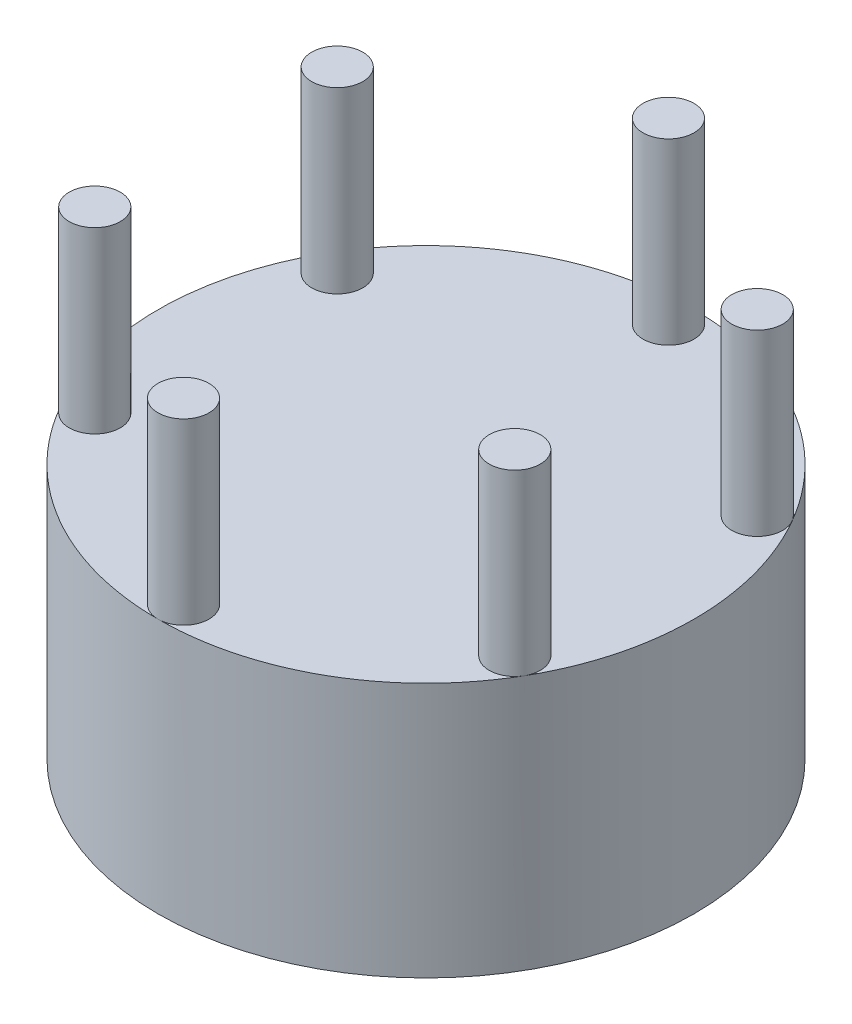
SolidWorks part; units mm, degrees
material "1060 Alloy"
ref_plane "Front Plane" through (0, 0, 0) normal (0, 0, 1) x (1, 0, 0)
ref_plane "Top Plane" through (0, 0, 0) normal (0, 1, 0) x (1, 0, 0)
ref_plane "Right Plane" through (0, 0, 0) normal (1, 0, 0) x (0, 0, -1)
sketch "Sketch1" plane through (0, 0, 0) normal (0, 1, 0) x (1, 0, 0)
  circle A0 centre (0, 0) radius 21
  dimension "D1" = 42
extrude "Boss-Extrude1" add sketch "Sketch1" along normal blind 20
sketch "Sketch2" plane through (0, 20, 0) normal (0, 1, 0) x (1, 0, 0)
  circle A0 centre (0, -19) radius 2
  dimension "D2" = 4
  dimension "D1" = 19
extrude "Boss-Extrude3" add sketch "Sketch2" along normal blind 14
sketch "Sketch3" plane through (0, 0, 0) normal (0, 0, 1) x (1, 0, 0)
  line L0 (0, 0) -> (0, 39.2101) construction
pattern_circular "CirPattern1" count 6 over 360 about axis through (0, 0, 0) along (0, 1, 0) of "Boss-Extrude3"
